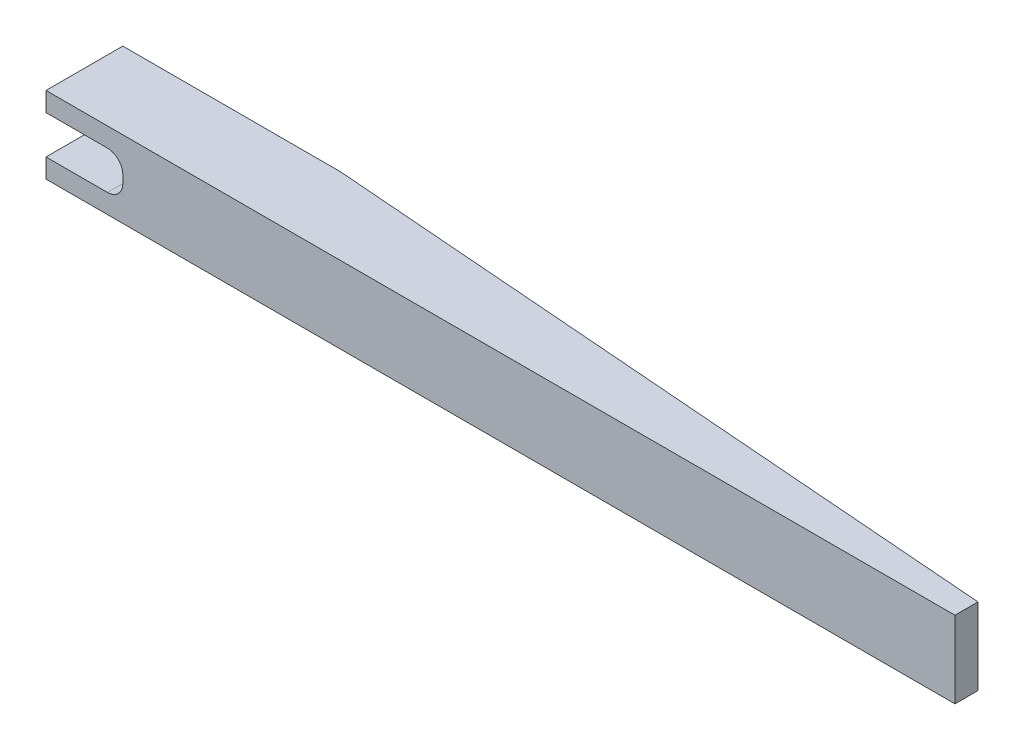
SolidWorks part; units mm, degrees
ref_plane "Alzado" through (0, 0, 0) normal (0, 0, 1) x (1, 0, 0)
ref_plane "Planta" through (0, 0, 0) normal (0, 1, 0) x (1, 0, 0)
ref_plane "Vista lateral" through (0, 0, 0) normal (1, 0, 0) x (0, 0, -1)
sketch "Croquis1" plane through (0, 0, 0) normal (0, 0, 1) x (1, 0, 0)
  line L1 (-59.175, 5) -> (59.175, 5)
  line L2 (-59.175, 5) -> (-59.175, -5)
  line L3 (-59.175, -5) -> (59.175, -5)
  line L4 (59.175, 5) -> (59.175, -5)
  line L5 (-59.175, 5) -> (59.175, -5) construction
  line L6 (-59.175, -5) -> (59.175, 5) construction
  point P0 (0, 0)
  dimension "D1" = 118.35
  dimension "D2" = 10
extrude "Saliente-Extruir1" add sketch "Croquis1" along normal blind 10
sketch "Croquis2" plane through (0, 0, 10) normal (0, 0, 1) x (1, 0, 0)
  line L0 (-59.175, 5) -> (-59.175, -5) construction
  line L1 (-69.175, 2.5) -> (-49.175, 2.5)
  line L2 (-69.175, 2.5) -> (-69.175, -2.5)
  line L3 (-69.175, -2.5) -> (-49.175, -2.5)
  line L4 (-49.175, 2.5) -> (-49.175, -2.5)
  line L5 (-69.175, 2.5) -> (-49.175, -2.5) construction
  line L6 (-69.175, -2.5) -> (-49.175, 2.5) construction
  point P0 (-59.175, 0)
  dimension "D1" = 20
  dimension "D2" = 5
extrude "Cortar-Extruir1" cut sketch "Croquis2" against normal through all
sketch "Croquis3" plane through (0, 5, 0) normal (0, 1, 0) x (1, 0, 0)
  line L0 (59.175, -7) -> (-30.825, 0)
  line L1 (59.175, -10) -> (59.175, 0) construction
  line L2 (59.175, 0) -> (-59.175, 0) construction
  line L3 (-30.825, 0) -> (59.175, 0)
  line L4 (59.175, 0) -> (59.175, -7)
  dimension "D1" = 90
  dimension "D2" = 7
extrude "Cortar-Extruir2" cut sketch "Croquis3" against normal through all
fillet "Redondeo1" radius 2 2 edges at (-49.175, 2.5, 5) (-49.175, -2.5, 5)
